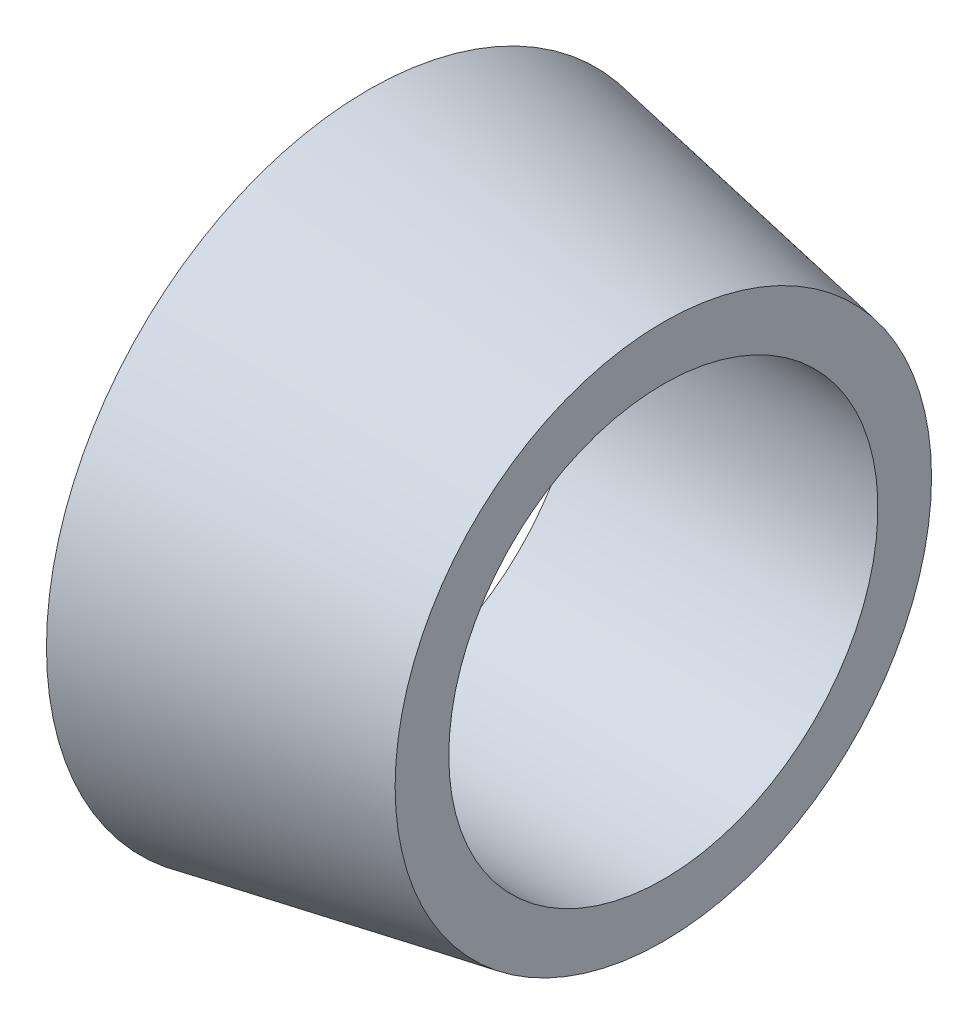
SolidWorks part; units mm, degrees
ref_plane "Płaszczyzna XY" through (0, 0, 0) normal (0, 0, 1) x (1, 0, 0)
ref_plane "Płaszczyzna XZ" through (0, 0, 0) normal (0, 1, 0) x (1, 0, 0)
ref_plane "Płaszczyzna YZ" through (0, 0, 0) normal (1, 0, 0) x (0, 0, -1)
sketch "Szkic1" plane through (0, 0, 0) normal (0, 0, 1) x (1, 0, 0)
  line L0 (0, 4) -> (0, 6)
  line L1 (0, 6) -> (5.5, 5)
  line L2 (5.5, 5) -> (5.5, 4)
  line L3 (5.5, 4) -> (0, 4)
  line L4 (0, 0) -> (11.0944, 0) construction
  dimension "D1" = 5.5
  dimension "D2" = 4
  dimension "D3" = 6
  dimension "D4" = 1
revolve "Obrót1" add sketch "Szkic1" angle 360 about L4
